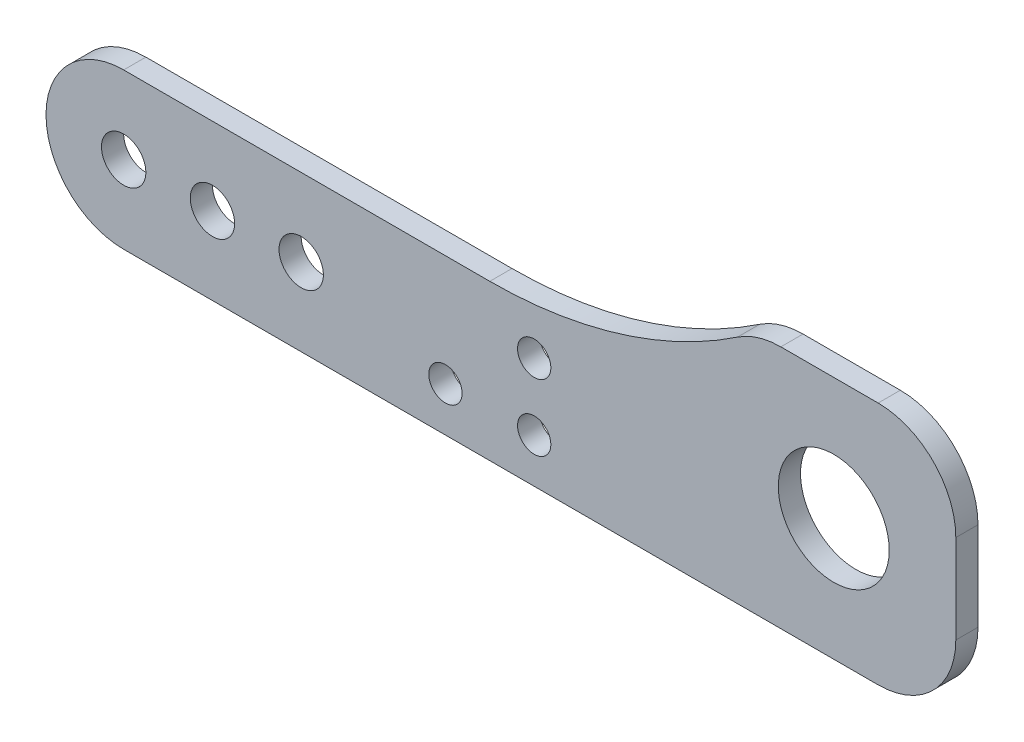
SolidWorks part; units mm, degrees
ref_plane "Front Plane" through (0, 0, 0) normal (0, 0, 1) x (1, 0, 0)
ref_plane "Top Plane" through (0, 0, 0) normal (0, 1, 0) x (1, 0, 0)
ref_plane "Right Plane" through (0, 0, 0) normal (1, 0, 0) x (0, 0, -1)
sketch "Sketch1" plane through (0, 0, 0) normal (0, 0, 1) x (1, 0, 0)
  line L0 (0, 7) -> (33, 7)
  line L1 (68, -7) -> (0, -7)
  line L5 (59.2298, 15) -> (68, 15)
  line L6 (75, 0) -> (75, 8)
  arc A1 (0, -7) -> (0, 7) centre (0, 0) cw
  arc A2 (33, 7) -> (55.3232, 13.8085) centre (33, 47) ccw
  arc A3 (68, -7) -> (75, 0) centre (68, 0) ccw
  arc A4 (68, 15) -> (75, 8) centre (68, 8) cw
  arc A5 (59.2298, 15) -> (55.3232, 13.8085) centre (59.2298, 8) ccw
  point P3 (75, -7)
  point P15 (75, 15)
  point P18 (57, 15)
  dimension "D2" = 7
  dimension "D4" = 40
  dimension "D1" = 7
  dimension "D3" = 22
  dimension "D5" = 18
  dimension "D6" = 75
extrude "Boss-Extrude1" add sketch "Sketch1" along normal blind 2
sketch "Sketch2" plane through (0, 0, 2) normal (0, 0, 1) x (1, 0, 0)
  line L0 (-7, 0) -> (-7, -7) construction
  line L6 (0, 0) -> (8, 0) construction
  line L7 (8, 0) -> (16, 0) construction
  line L8 (-7, -7) -> (0, -7) construction
  circle A0 centre (0, 0) radius 2
  circle A2 centre (8, 0) radius 2
  circle A5 centre (16, 0) radius 2
  arc A6 (0, 7) -> (0, -7) centre (0, 0) ccw construction
  dimension "D1" = 4
  dimension "D2" = 8
extrude "Cut-Extrude1" cut sketch "Sketch2" against normal up to surface (2 mm away) up to face at (47.7635, 5.6039, 0)
sketch "Sketch3" plane through (0, 0, 2) normal (0, 0, 1) x (1, 0, 0)
  line L0 (75, 0) -> (75, 8) construction
  line L2 (64, 4) -> (75, 4) construction
  line L3 (64, 4) -> (64, -7) construction
  line L4 (0, -7) -> (68, -7) construction
  circle A0 centre (64, 4) radius 5
  dimension "D1" = 10
extrude "Cut-Extrude2" cut sketch "Sketch3" against normal up to surface (2 mm away) up to face at (2, 0, 0)
hole_wizard "Ø3.0mm Dowel Hole2" positions "Sketch9" profile "Sketch10" hole size "Ø3.0" standard "ANSI Metric" end condition through all
sketch "Sketch9" plane through (0, 0, 2) normal (0, 0, 1) x (1, 0, 0)
  line L2 (75, 0) -> (75, 8) construction
  line L3 (0, -7) -> (68, -7) construction
  point P0 (29, -3)
  point P3 (37, -3)
  point P6 (37, 3)
  dimension "D1" = 6
  dimension "D2" = 8
  dimension "D3" = 38
  dimension "D4" = 4
sketch "Sketch10" plane through (29, -3, 2) normal (1, 0, 0) x (0, -1, 0)
  line L0 (0, 0) -> (0, 2)
  line L1 (0, 2) -> (1.5, 2)
  line L2 (1.5, 2) -> (1.5, 0)
  line L5 (1.5, 0) -> (0, 0)
  line L11 (0, -6.35) -> (0, 107.95) construction
  dimension "Thru Hole Dia." = 3
  dimension "Thru Hole Depth" = 2
sketch "Sketch4" plane through (0, 0, 2) normal (0, 0, -1) x (-1, 0, 0)
  line L0 (0, -7) -> (-68, -7) construction
  line L1 (-49, -7) -> (-23, -7)
  line L2 (-49, -7) -> (-49, 10.3394)
  line L3 (-49, 10.3394) -> (-23, 10.3394)
  line L4 (-23, -7) -> (-23, 10.3394)
  line L5 (-75, 0) -> (-75, 8) construction
  arc A0 (-55.3232, 13.8085) -> (-33, 7) centre (-33, 47) ccw construction
  dimension "D1" = 26
  dimension "D2" = 26
extrude "Cut-Extrude3" [suppressed] cut sketch "Sketch4" along normal blind 1.6
